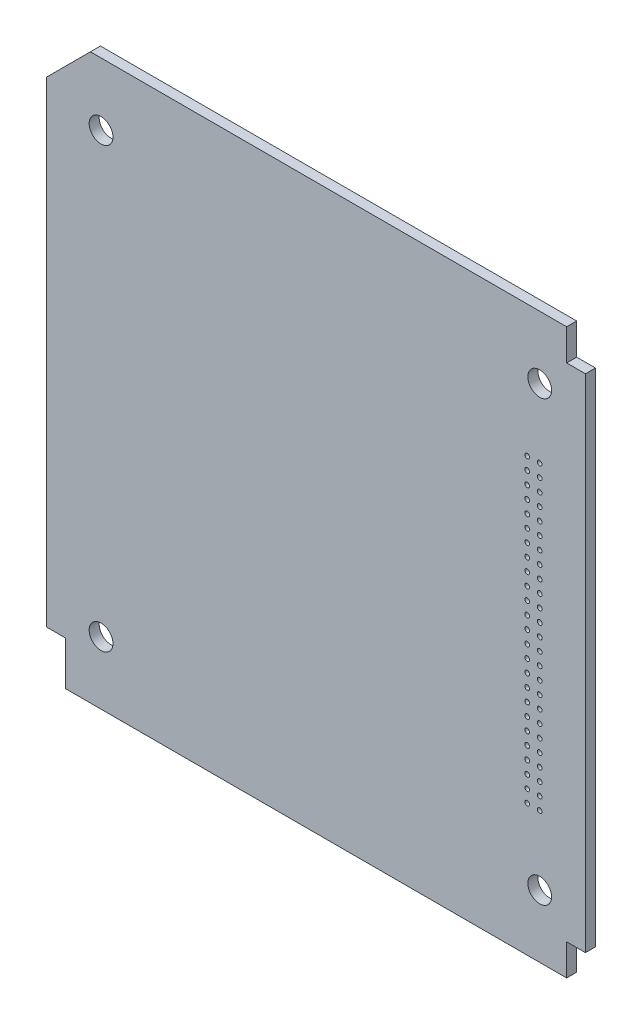
SolidWorks part; units mm, degrees
material "電力回路基板"
ref_plane "正面" through (0, 0, 0) normal (0, 0, 1) x (1, 0, 0)
ref_plane "平面" through (0, 0, 0) normal (0, 1, 0) x (1, 0, 0)
ref_plane "右側面" through (0, 0, 0) normal (1, 0, 0) x (0, 0, -1)
sketch "Sketch1" plane through (0, 0, 0) normal (0, 0, 1) x (1, 0, 0)
  line L0 (-3, 0) -> (-86, 0)
  line L4 (-86, 0) -> (-86, -90)
  line L7 (0, -5) -> (-3, -5)
  line L8 (-3, 0) -> (-3, -5)
  line L11 (0, -85) -> (-3, -85)
  line L12 (-3, -90) -> (-3, -85)
  line L13 (0, -5) -> (0, -85)
  line L14 (-3, -90) -> (-86, -90)
  circle A0 centre (-7.3, -10) radius 1.9
  circle A1 centre (-77.3, -10) radius 1.9
  circle A2 centre (-77.3, -80) radius 1.9
  circle A3 centre (-7.3, -80) radius 1.9
  circle A4 centre (-9.3, -69) radius 0.375
  circle A5 centre (-7.3, -69) radius 0.375
  circle A6 centre (-7.3, -67) radius 0.375
  circle A7 centre (-9.3, -67) radius 0.375
  circle A8 centre (-9.3, -65) radius 0.375
  circle A9 centre (-7.3, -65) radius 0.375
  circle A10 centre (-7.3, -63) radius 0.375
  circle A11 centre (-9.3, -63) radius 0.3838
  circle A12 centre (-9.3, -61) radius 0.375
  circle A13 centre (-7.3, -61) radius 0.375
  circle A14 centre (-7.3, -59) radius 0.375
  circle A15 centre (-9.3, -59) radius 0.375
  circle A16 centre (-7.3, -57) radius 0.375
  circle A17 centre (-9.3, -57) radius 0.375
  circle A18 centre (-9.3, -55) radius 0.375
  circle A19 centre (-7.3, -55) radius 0.375
  circle A20 centre (-7.3, -53) radius 0.375
  circle A21 centre (-9.3, -53) radius 0.375
  circle A22 centre (-9.3, -51) radius 0.375
  circle A23 centre (-7.3, -51) radius 0.375
  circle A24 centre (-7.3, -49) radius 0.375
  circle A25 centre (-9.3, -49) radius 0.375
  circle A26 centre (-9.3, -47) radius 0.375
  circle A27 centre (-7.3, -47) radius 0.375
  circle A28 centre (-7.3, -45) radius 0.375
  circle A29 centre (-9.3, -45) radius 0.3842
  circle A30 centre (-9.3, -43) radius 0.375
  circle A31 centre (-7.3, -43) radius 0.3808
  circle A32 centre (-7.3, -41) radius 0.3774
  circle A33 centre (-9.3, -41) radius 0.3774
  circle A34 centre (-9.3, -39) radius 0.375
  circle A35 centre (-7.3, -39) radius 0.375
  circle A36 centre (-7.3, -37) radius 0.375
  circle A37 centre (-9.3, -37) radius 0.3808
  circle A38 centre (-7.3, -35) radius 0.375
  circle A39 centre (-9.3, -35) radius 0.375
  circle A40 centre (-9.3, -33) radius 0.375
  circle A41 centre (-7.3, -33) radius 0.375
  circle A42 centre (-7.3, -31) radius 0.375
  circle A43 centre (-9.3, -31) radius 0.375
  circle A44 centre (-7.3, -29) radius 0.375
  circle A45 centre (-9.3, -29) radius 0.375
  circle A46 centre (-9.3, -27) radius 0.375
  circle A47 centre (-7.3, -27) radius 0.375
  circle A48 centre (-7.3, -25) radius 0.375
  circle A49 centre (-9.3, -25) radius 0.375
  circle A50 centre (-7.3, -23) radius 0.375
  circle A51 centre (-9.3, -23) radius 0.375
  circle A52 centre (-9.3, -21) radius 0.375
  circle A53 centre (-7.3, -21) radius 0.375
  dimension "D5" = 70
  dimension "D6" = 3
  dimension "D3" = 3.8
  dimension "D10" = 7.3
  dimension "D14" = 10
  dimension "D15" = 10
  dimension "D2" = 90
  dimension "D4" = 70
  dimension "D7" = 5
  dimension "D8" = 86
  dimension "D9" = 7.3
  dimension "D11" = 3
  dimension "D12" = 5
  dimension "D13" = 9.3
  dimension "D16" = 21
extrude "Boss-Extrude1" add sketch "Sketch1" along normal blind 1.6
sketch "ｽｹｯﾁ1" plane through (0, 0, 1.6) normal (0, 0, 1) x (1, 0, 0)
  line L0 (-86, -90) -> (-86, -83)
  line L11 (-86, -83) -> (-83, -83)
  line L12 (-83, -83) -> (-83, -90)
  line L13 (-83, -90) -> (-86, -90)
  line L14 (-86, 0) -> (-86, -7)
  line L15 (-86, -7) -> (-79, 0)
  line L16 (-79, 0) -> (-86, 0)
extrude "ｶｯﾄ - 押し出し1" cut sketch "ｽｹｯﾁ1" against normal blind 10
